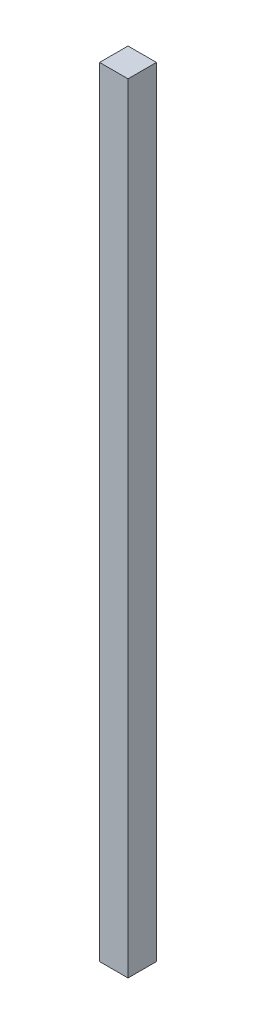
SolidWorks part; units mm, degrees
ref_plane "Plan de face" through (0, 0, 0) normal (0, 0, 1) x (1, 0, 0)
ref_plane "Plan de dessus" through (0, 0, 0) normal (0, 1, 0) x (1, 0, 0)
ref_plane "Plan de droite" through (0, 0, 0) normal (1, 0, 0) x (0, 0, -1)
sketch "Esquisse1" plane through (0, 0, 0) normal (0, 0, 1) x (1, 0, 0)
  line L1 (-51.4239, 37.1959) -> (-41.4239, 37.1959)
  line L2 (-51.4239, 37.1959) -> (-51.4239, -236.8041)
  line L3 (-51.4239, -236.8041) -> (-41.4239, -236.8041)
  line L4 (-41.4239, 37.1959) -> (-41.4239, -236.8041)
  dimension "D1" = 10
  dimension "D2" = 274
extrude "Boss.-Extru.1" add sketch "Esquisse1" along normal blind 10 contours L2 L3 L4 L1
equation "\"EpaisseurPlaque\"= 3"
equation "\"ProfondeurBoite\"=460"
equation "\"LongueurSyphon\"=270"
equation "\"LargeurSyphon\"=120"
equation "\"HauteurCoteDroit\"= 490"
equation "\"HauteurCoteGauche\"= 540"
equation "\"HauteurSolSyphon\"= 300"
equation "\"HauteurSyphon\"=\"HauteurCoteGauche\"-\"HauteurSolSyphon\""
equation "\"LargeurDroite\"=10"
equation "\"LargeurGauche\"=150"
equation "\"LargeurBoite\"= \"LargeurDroite\" + \"LargeurGauche\" + \"LargeurSyphon\""
equation "\"D2@Esquisse1\"=\"HauteurCoteGauche\" - \"HauteurSyphon\" - 20 - 6"
